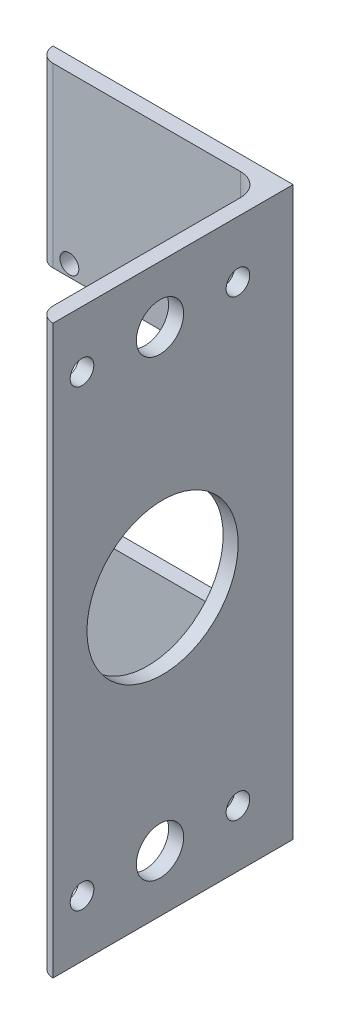
SolidWorks part; units mm, degrees
ref_plane "Alzado" through (0, 0, 0) normal (0, 0, 1) x (1, 0, 0)
ref_plane "Planta" through (0, 0, 0) normal (0, 1, 0) x (1, 0, 0)
ref_plane "Vista lateral" through (0, 0, 0) normal (1, 0, 0) x (0, 0, -1)
sketch "Croquis1" plane through (0, 0, 0) normal (0, 0, 1) x (1, 0, 0)
  line L0 (0, 0) -> (0, 120)
  dimension "D1" = 120
other "Hierro angular 2 X 2 X 0.125(1)"
ref_plane "Plano1" through (0, 0, 0) normal (0, 1, 0) x (-1, 0, 0)
sketch "Sketch1" plane through (0, 0, 0) normal (0, 1, 0) x (-1, 0, 0)
  line L0 (0, 0) -> (0, 50.8)
  line L1 (0, 50.8) -> (0.0051, 50.8)
  line L2 (3.175, 47.6301) -> (3.175, 7.9375)
  line L3 (7.9375, 3.175) -> (47.6301, 3.175)
  line L4 (50.8, 0.0051) -> (50.8, 0)
  line L5 (50.8, 0) -> (0, 0)
  arc A0 (50.8, 0.0051) -> (47.6301, 3.175) centre (47.6301, 0.0051) ccw
  arc A1 (0.0051, 50.8) -> (3.175, 47.6301) centre (0.0051, 47.6301) cw
  arc A2 (7.9375, 3.175) -> (3.175, 7.9375) centre (7.9375, 7.9375) cw
  point P10 (25.4, 0)
  point P14 (0, 25.4)
  point P15 (3.175, 25.4)
  point P16 (25.4, 3.175)
  point P17 (3.175, 50.8)
  point P18 (50.8, 3.175)
  point P19 (0, 0)
  dimension "D2" = 0.0051
  dimension "Radius_1" = 4.7625
  dimension "D1" = 3.175
  dimension "H_leg" = 50.8
sketch "Croquis3" plane through (0, 0, 0) normal (0, 0, -1) x (-1, 0, 0)
  line L0 (3.175, 120) -> (3.175, 0) construction
  line L1 (3.175, 120) -> (3.175, 0) construction
  line L2 (50.8, 60) -> (3.175, 60) construction
  line L3 (50.8, 120) -> (50.8, 0) construction
  line L5 (3.175, 82.5) -> (50.8, 82.5)
  line L6 (3.175, 82.5) -> (3.175, 37.5)
  line L7 (3.175, 37.5) -> (50.8, 37.5)
  line L8 (50.8, 82.5) -> (50.8, 37.5)
  line L9 (3.175, 82.5) -> (50.8, 37.5) construction
  line L10 (3.175, 37.5) -> (50.8, 82.5) construction
  point P6 (26.9875, 60)
  dimension "D1" = 45
extrude "Cortar-Extruir1" cut sketch "Croquis3" against normal blind 10
sketch "Croquis4" plane through (-3.175, 0, 0) normal (-1, 0, 0) x (0, 0, 1)
  line L0 (47.6301, 60) -> (0, 60) construction
  line L1 (47.6301, 120) -> (47.6301, 0) construction
  line L2 (0, 82.5) -> (0, 37.5) construction
  line L3 (3.175, 37.5) -> (3.175, 0) construction
  line L4 (3.175, 37.5) -> (3.175, 0)
  line L5 (3.175, 12) -> (66.2986, 12) construction
  line L6 (28.175, 0) -> (28.175, 21.3337) construction
  line L7 (7.9375, 0) -> (47.6301, 0) construction
  line L8 (44.675, 12) -> (11.675, 12) construction
  circle A0 centre (28.175, 12) radius 5
  circle A1 centre (11.675, 12) radius 2.5
  circle A2 centre (44.675, 12) radius 2.5
  circle A3 centre (44.675, 108) radius 2.5
  circle A4 centre (28.175, 108) radius 5
  circle A5 centre (11.675, 108) radius 2.5
  point P19 (28.175, 12)
  dimension "D3" = 5
  dimension "D4" = 10
  dimension "D1" = 12
  dimension "D2" = 25
  dimension "D5" = 33
extrude "Cortar-Extruir2" cut sketch "Croquis4" against normal blind 10 contours A0 | A1 | A2 | A3 | A4 | A5
sketch "Croquis5" plane through (-3.175, 0, 0) normal (-1, 0, 0) x (0, 0, 1)
  line L1 (27.6301, 0) -> (27.6301, 120) construction
  line L2 (7.9375, 0) -> (47.6301, 0) construction
  line L3 (7.9375, 120) -> (47.6301, 120) construction
  line L4 (47.6301, 120) -> (47.6301, 0) construction
  circle A0 centre (27.6301, 60) radius 16
  dimension "D2" = 32
  dimension "D1" = 20
extrude "Cortar-Extruir3" cut sketch "Croquis5" against normal up to surface (3.175 mm away) up to face at (0, 12, 14.175)
sketch "Croquis6" plane through (0, 0, 0) normal (0, 0, -1) x (-1, 0, 0)
  circle A0 centre (14.175, 35) radius 2 construction
  circle A1 centre (14.175, 85) radius 2 construction
  circle A2 centre (44.175, 85) radius 2 construction
  circle A3 centre (14.175, 35) radius 2
  circle A4 centre (14.175, 85) radius 2
  circle A5 centre (44.175, 85) radius 2
  circle A6 centre (44.175, 35) radius 2 construction
  circle A7 centre (44.175, 35) radius 2
extrude "Cortar-Extruir4" cut sketch "Croquis6" against normal up to surface (3.175 mm away) up to face at (-27.7838, 101.25, 3.175)
